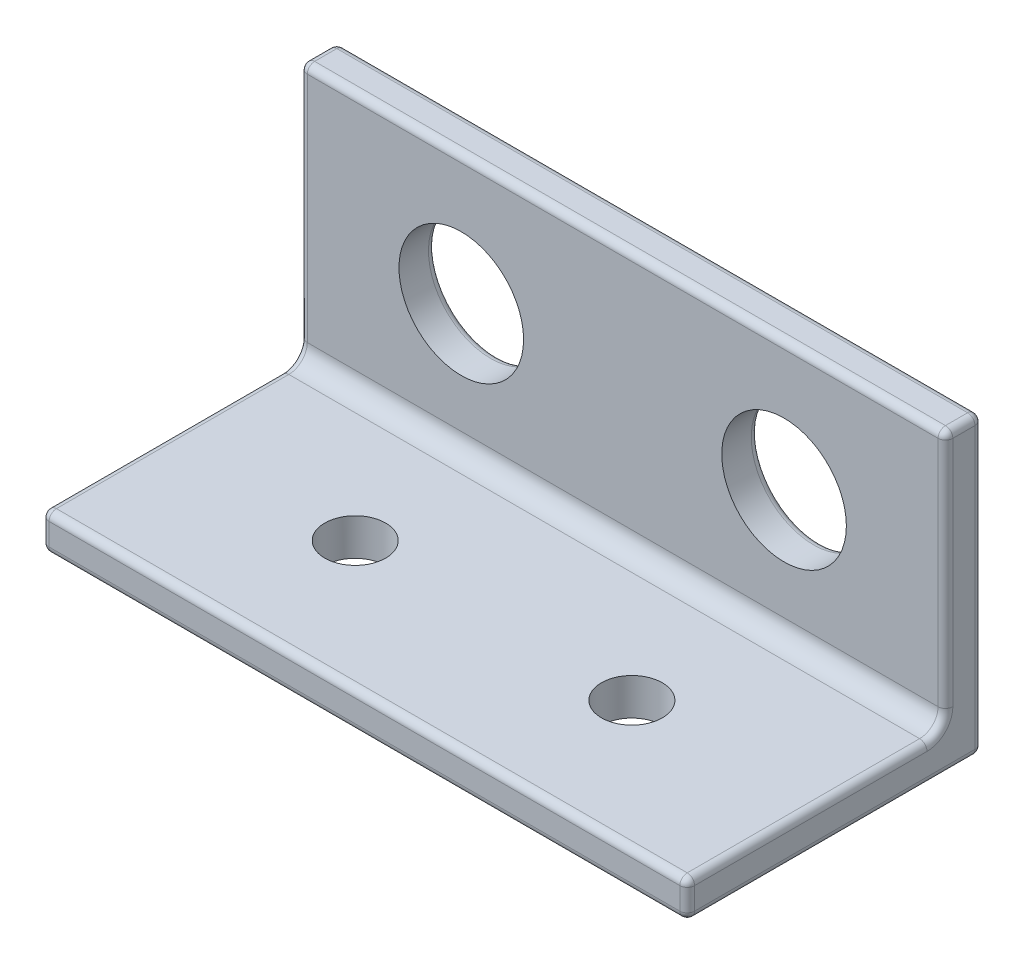
SolidWorks part; units mm, degrees
ref_plane "Front" through (0, 0, 0) normal (0, 0, 1) x (1, 0, 0)
ref_plane "Top" through (0, 0, 0) normal (0, 1, 0) x (1, 0, 0)
ref_plane "Right" through (0, 0, 0) normal (1, 0, 0) x (0, 0, -1)
sketch "Sketch1" plane through (0, 0, 0) normal (1, 0, 0) x (0, 0, -1)
  line L0 (-2, 16) -> (0, 16)
  line L1 (0, 16) -> (0, 0)
  line L2 (0, 0) -> (-16, 0)
  line L3 (-16, 0) -> (-16, 2)
  line L4 (-16, 2) -> (-2, 2)
  line L5 (-2, 2) -> (-2, 16)
  dimension "D1" = 2
  dimension "D2" = 14
  dimension "D3" = 14
extrude "Mount" add sketch "Sketch1" along normal mid plane 35
hole_wizard "1/4\" Antenna Holes" positions "Sketch2" profile "Sketch3" hole size "1/4" standard "ANSI Inch" end condition through all
sketch "Sketch2" plane through (0, 0, 2) normal (0, 0, 1) x (1, 0, 0)
  line L0 (0, 2) -> (0, 16) construction
  line L1 (17.5, 2) -> (-17.5, 2) construction
  line L2 (17.5, 16) -> (-17.5, 16) construction
  line L8 (0, 9) -> (-17.5, 9) construction
  line L9 (-17.5, 16) -> (-17.5, 2) construction
  point P0 (-8.75, 9)
  point P30 (8.75, 9)
sketch "Sketch3" plane through (-8.75, 9, 2) normal (1, 0, 0) x (0, -1, 0)
  line L0 (0, 0) -> (0, 2)
  line L1 (0, 2) -> (3.3782, 2)
  line L2 (3.3782, 2) -> (3.3782, 0)
  line L5 (3.3782, 0) -> (0, 0)
  line L11 (0, -6.35) -> (0, 107.95) construction
  dimension "Thru Hole Dia." = 6.7564
  dimension "Thru Hole Depth" = 2
sketch "Sketch6" plane through (0, 2, 0) normal (0, 1, 0) x (1, 0, 0)
  line L0 (0, -2) -> (0, -16) construction
  line L1 (17.5, -2) -> (-17.5, -2) construction
  line L2 (17.5, -16) -> (-17.5, -16) construction
  line L3 (-17.5, -9) -> (0, -9) construction
  line L4 (-17.5, -2) -> (-17.5, -16) construction
  circle A0 centre (-7.5, -9) radius 1.65
  circle A1 centre (7.5, -9) radius 1.65
  point P14 (-6.4465, -9)
  point P15 (-7.2283, -9)
  dimension "D1" = 3.3
  dimension "D2" = 15
extrude "M3 Standoff Holes" cut sketch "Sketch6" against normal through all both and the other way through all
fillet "Inside Fillet" radius 1 1 edges at (0, 2, 2)
fillet "External Fillets" radius 0.4 21 edges at (0, 0, 0) (12.1282, 9, 0) (-5.3718, 9, 0) (0, 16, 0) (0, 16, 2) (-17.5, 2.2929, 2.2929) (-17.5, 2, 9.5) (-17.5, 0, 8) (-17.5, 8, 0) (-17.5, 16, 1) (-17.5, 9.5, 2) (0, 2, 16) (0, 0, 16) (-17.5, 1, 16) (17.5, 16, 1) (17.5, 8, 0) (17.5, 0, 8) (17.5, 1, 16) (17.5, 2, 9.5) (17.5, 2.2929, 2.2929) (17.5, 9.5, 2)
